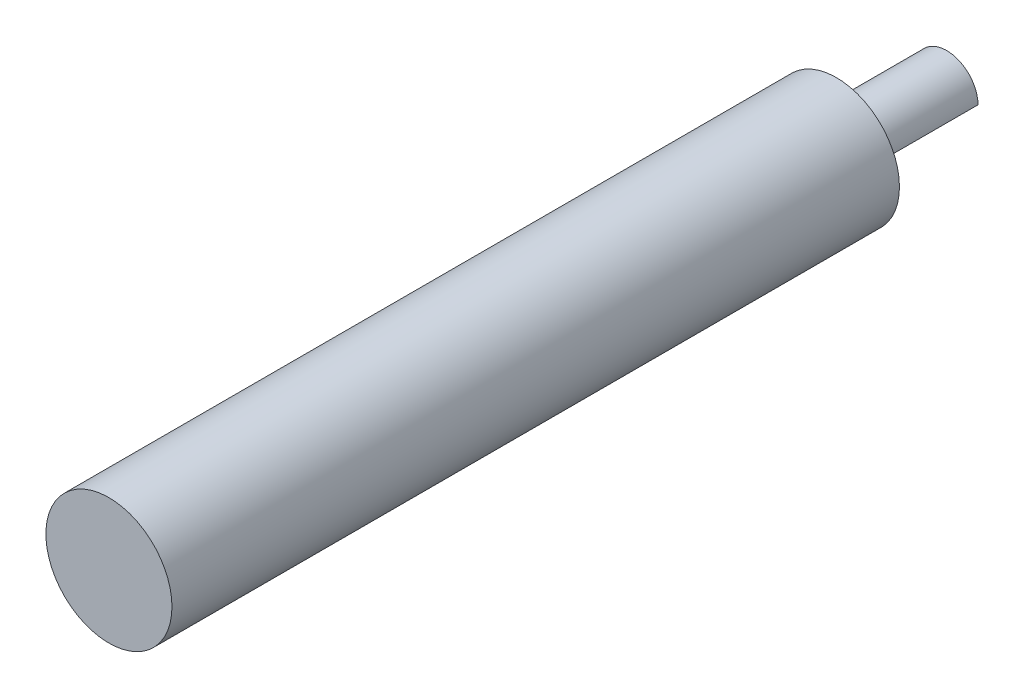
SolidWorks part; units mm, degrees
material "AISI 1020 Steel, Cold Rolled"
ref_plane "Front Plane" through (0, 0, 0) normal (0, 0, 1) x (1, 0, 0)
ref_plane "Top Plane" through (0, 0, 0) normal (0, 1, 0) x (1, 0, 0)
ref_plane "Right Plane" through (0, 0, 0) normal (1, 0, 0) x (0, 0, -1)
sketch "Sketch1" plane through (0, 0, 0) normal (0, 0, 1) x (1, 0, 0)
  circle A0 centre (0, 0) radius 3.1623
  dimension "D1" = 6.3246
extrude "Boss-Extrude1" add sketch "Sketch1" along normal blind 11.0998
sketch "Sketch2" plane through (0, 0, 0) normal (0, 0, -1) x (-1, 0, 0)
  line L0 (0.0012, -3.1623) -> (-3.1623, 0.0012)
  circle A0 centre (0, 0) radius 3.1623 construction
  dimension "D1" = 2.2352
extrude "Cut-Extrude1" cut sketch "Sketch2" against normal through all and the other way through all
sketch "Sketch3" plane through (0, 0, 11.0998) normal (0, 0, 1) x (1, 0, 0)
  circle A0 centre (0, 0) radius 6.35
  dimension "D1" = 12.7
extrude "Boss-Extrude2" add sketch "Sketch3" along normal blind 73.279
sketch "Sketch5" plane through (0, 0, 84.3788) normal (0, 0, 1) x (1, 0, 0)
  circle A0 centre (0, 0) radius 6.35
fillet "Fillet1" [suppressed] radius 1.27
